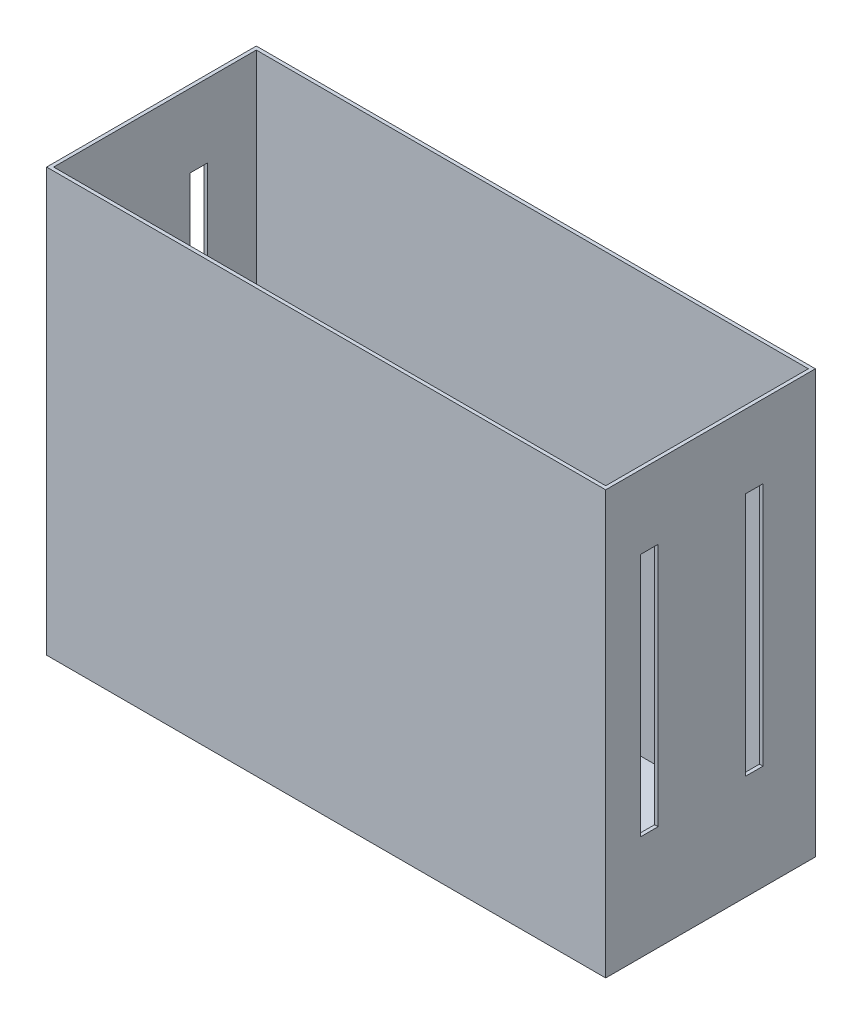
SolidWorks part; units mm, degrees
ref_plane "Front Plane" through (0, 0, 0) normal (0, 0, 1) x (1, 0, 0)
ref_plane "Top Plane" through (0, 0, 0) normal (0, 1, 0) x (1, 0, 0)
ref_plane "Right Plane" through (0, 0, 0) normal (1, 0, 0) x (0, 0, -1)
sketch "Sketch1" plane through (0, 0, 0) normal (0, 1, 0) x (1, 0, 0)
  line L0 (-200.66, 73.66) -> (200.66, 73.66)
  line L1 (-203.2, 76.2) -> (203.2, 76.2)
  line L2 (-203.2, 76.2) -> (-203.2, -76.2)
  line L3 (-203.2, -76.2) -> (203.2, -76.2)
  line L4 (203.2, 76.2) -> (203.2, -76.2)
  line L5 (-203.2, 76.2) -> (203.2, -76.2) construction
  line L6 (-203.2, -76.2) -> (203.2, 76.2) construction
  line L7 (200.66, 73.66) -> (200.66, -73.66)
  line L8 (-200.66, -73.66) -> (200.66, -73.66)
  line L9 (-200.66, 73.66) -> (-200.66, -73.66)
  point P4 (0, 0)
  dimension "D1" = 406.4
  dimension "D2" = 152.4
  dimension "D3" = 2.54
extrude "Boss-Extrude1" add sketch "Sketch1" along normal blind 304.8
sketch "Sketch2" plane through (0, 0, 0) normal (0, -1, 0) x (1, 0, 0)
  line L0 (203.2, 76.2) -> (203.2, -76.2) construction
  line L1 (-203.2, -76.2) -> (-203.2, 76.2) construction
  line L2 (-203.2, 76.2) -> (203.2, 76.2) construction
  line L3 (203.2, -76.2) -> (-203.2, -76.2) construction
  line L4 (203.2, 76.2) -> (203.2, -76.2)
  line L5 (-203.2, -76.2) -> (-203.2, 76.2)
  line L6 (-203.2, 76.2) -> (203.2, 76.2)
  line L7 (203.2, -76.2) -> (-203.2, -76.2)
extrude "Boss-Extrude2" add sketch "Sketch2" along normal blind 2.54
sketch "Sketch3" plane through (-203.2, 0, 0) normal (-1, 0, 0) x (0, 0, 1)
  line L0 (76.2, 304.8) -> (76.2, -2.54) construction
  line L1 (38.1, 251.46) -> (50.8, 251.46)
  line L2 (38.1, 251.46) -> (38.1, 73.66)
  line L3 (38.1, 73.66) -> (50.8, 73.66)
  line L4 (50.8, 251.46) -> (50.8, 73.66)
  line L5 (38.1, 251.46) -> (50.8, 73.66) construction
  line L6 (38.1, 73.66) -> (50.8, 251.46) construction
  line L7 (76.2, -2.54) -> (-76.2, -2.54) construction
  line L8 (38.1, 251.46) -> (-25.4, 251.46) construction
  line L9 (38.1, 73.66) -> (-25.4, 73.66) construction
  line L11 (-25.4, 73.66) -> (-38.1, 73.66)
  line L12 (-25.4, 73.66) -> (-25.4, 251.46)
  line L13 (-25.4, 251.46) -> (-38.1, 251.46)
  line L14 (-38.1, 73.66) -> (-38.1, 251.46)
  line L15 (-25.4, 73.66) -> (-38.1, 251.46) construction
  line L16 (-25.4, 251.46) -> (-38.1, 73.66) construction
  point P4 (44.45, 162.56)
  point P14 (-31.75, 162.56)
  dimension "D1" = 12.7
  dimension "D2" = 177.8
  dimension "D3" = 25.4
  dimension "D4" = 76.2
  dimension "D5" = 12.7
  dimension "D6" = 63.5
extrude "Cut-Extrude1" cut sketch "Sketch3" against normal through all both and the other way through all
